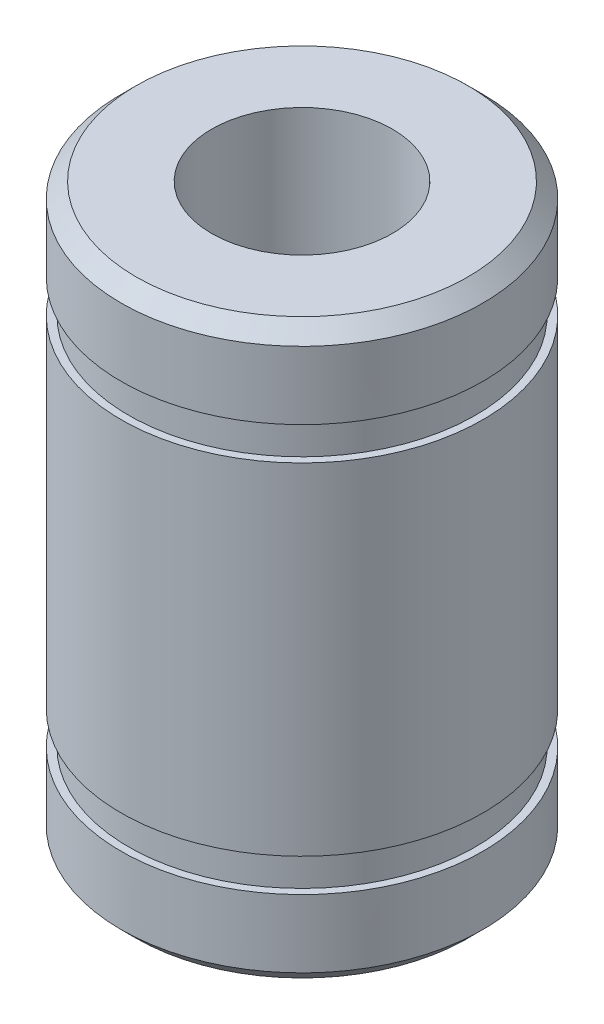
SolidWorks part; units mm, degrees
ref_plane "Front Plane" through (0, 0, 0) normal (0, 0, 1) x (1, 0, 0)
ref_plane "Top Plane" through (0, 0, 0) normal (0, 1, 0) x (1, 0, 0)
ref_plane "Right Plane" through (0, 0, 0) normal (1, 0, 0) x (0, 0, -1)
sketch "Sketch1" plane through (0, 0, 0) normal (0, 0, 1) x (1, 0, 0)
  line L0 (3, 0) -> (3, 9.5)
  line L1 (3, 9.5) -> (6, 9.5)
  line L2 (6, 9.5) -> (6, 6.75)
  line L3 (6, 6.75) -> (5.75, 6.75)
  line L4 (5.75, 6.75) -> (5.75, 5.65)
  line L5 (5.75, 5.65) -> (6, 5.65)
  line L6 (6, 5.65) -> (6, 0)
  line L7 (6, 0) -> (3, 0)
  line L8 (0, 0) -> (0, 9.5) construction
  line L9 (0, 0) -> (6, 0) construction
  point P11 (0, 48.4898)
  point P12 (5.875, 6.75)
  dimension "D1" = 1.1
  dimension "D2" = 19
  dimension "D3" = 13.5
  dimension "D4" = 6
  dimension "D5" = 12
  dimension "D6" = 11.5
revolve "Revolve1" add sketch "Sketch1" angle 360 about L8
chamfer "Chamfer1" distance 0.5 angle 45 1 edges at (0, 9.5, -6)
mirror "Mirror1" about plane through (6, 0, 0) normal (0, -1, 0) of bodies 101
